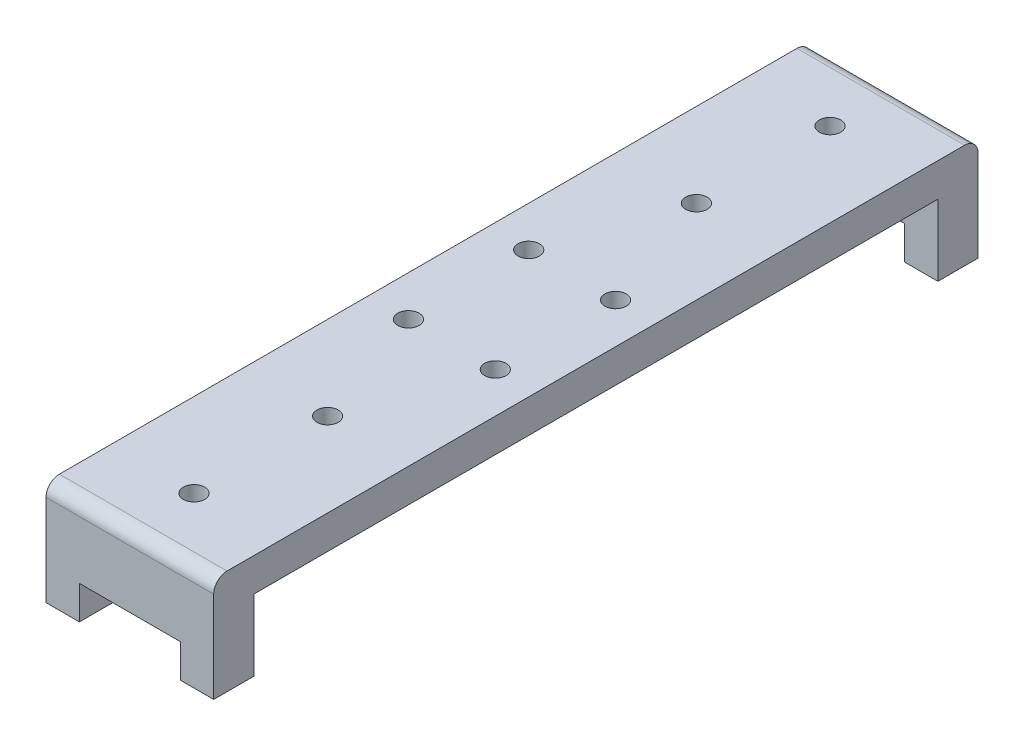
SolidWorks part; units mm, degrees
ref_plane "Front Plane" through (0, 0, 0) normal (0, 0, 1) x (1, 0, 0)
ref_plane "Top Plane" through (0, 0, 0) normal (0, 1, 0) x (1, 0, 0)
ref_plane "Right Plane" through (0, 0, 0) normal (1, 0, 0) x (0, 0, -1)
sketch "Sketch1" plane through (0, 0, 0) normal (0, 1, 0) x (1, 0, 0)
  line L0 (0, 51.2) -> (0, -47.8056) construction
  line L1 (-40.6489, 57.2) -> (55.7489, 57.2) construction
  line L2 (-7.55, 57.2) -> (-7.55, 51.2) construction
  line L3 (-7.55, 51.2) -> (7.55, 51.2) construction
  line L4 (7.55, 51.2) -> (7.55, 57.2) construction
  circle A0 centre (0, 27.6) radius 1.6
  circle A1 centre (-6.5, 9) radius 1.6
  circle A2 centre (6.5, 9) radius 1.6
  circle A3 centre (0, 47.6) radius 1.6
  dimension "D4" = 3.2
  dimension "D6" = 3.2
  dimension "D9" = 3.2
  dimension "D1" = 57.2
  dimension "D2" = 15.1
  dimension "D3" = 6
  dimension "D5" = 27.6
  dimension "D7" = 9
  dimension "D8" = 6.5
  dimension "D10" = 20
sketch "Sketch2" plane through (0, 0, 0) normal (0, 1, 0) x (1, 0, 0)
  line L0 (-40.6489, 57.2) -> (55.7489, 57.2) construction
  line L1 (-40.6489, 57.2) -> (55.7489, 57.2)
  line L2 (-7.55, 57.2) -> (-7.55, 51.2) construction
  line L3 (-12.55, 57.2) -> (12.55, 57.2)
  line L4 (-12.55, 57.2) -> (-12.55, 0)
  line L5 (-12.55, 0) -> (12.55, 0)
  line L6 (12.55, 57.2) -> (12.55, 0)
  circle A0 centre (0, 27.6) radius 1.6 construction
  circle A1 centre (0, 27.6) radius 1.6
  circle A2 centre (-6.5, 9) radius 1.6 construction
  circle A3 centre (6.5, 9) radius 1.6 construction
  circle A4 centre (-6.5, 9) radius 1.6
  circle A5 centre (6.5, 9) radius 1.6
  circle A6 centre (0, 47.6) radius 1.6 construction
  circle A7 centre (0, 47.6) radius 1.6
  dimension "D1" = 5
extrude "Boss-Extrude1" add sketch "Sketch2" along normal blind 5 contours L6 L1 L4 L5 A1
sketch "Sketch4" plane through (0, 0, -57.2) normal (0, 0, -1) x (-1, 0, 0)
  line L0 (0, 0) -> (0, -17.15) construction
  line L1 (-12.55, 0) -> (12.55, 0)
  line L2 (12.55, 0) -> (12.55, -10.65)
  line L3 (12.55, -10.65) -> (7.55, -10.65)
  line L4 (7.55, -10.65) -> (7.55, -5.65)
  line L5 (7.55, -5.65) -> (-7.55, -5.65)
  line L6 (-7.55, -5.65) -> (-7.55, -10.65)
  line L7 (-7.55, -10.65) -> (-12.55, -10.65)
  line L8 (-12.55, -10.65) -> (-12.55, 0)
  circle A0 centre (0, -17.15) radius 2.1445
  line M1 (-12.55, 0) -> (12.55, 0)
  dimension "D1" = 17.15
  dimension "D2" = 5
  dimension "D3" = 5
  dimension "D4" = 11.5
extrude "Boss-Extrude2" add sketch "Sketch4" against normal blind 6 contours L0 L8 L7 L6 L5 M1 | L1 L0 L5 L4 L3 L2
mirror "Mirror1" about plane through (0, 0, 0) normal (0, 0, 1) of "Boss-Extrude2", "Boss-Extrude1"
fillet "Fillet1" radius 2 2 edges at (0, 5, -57.2) (0, 5, 57.2)
